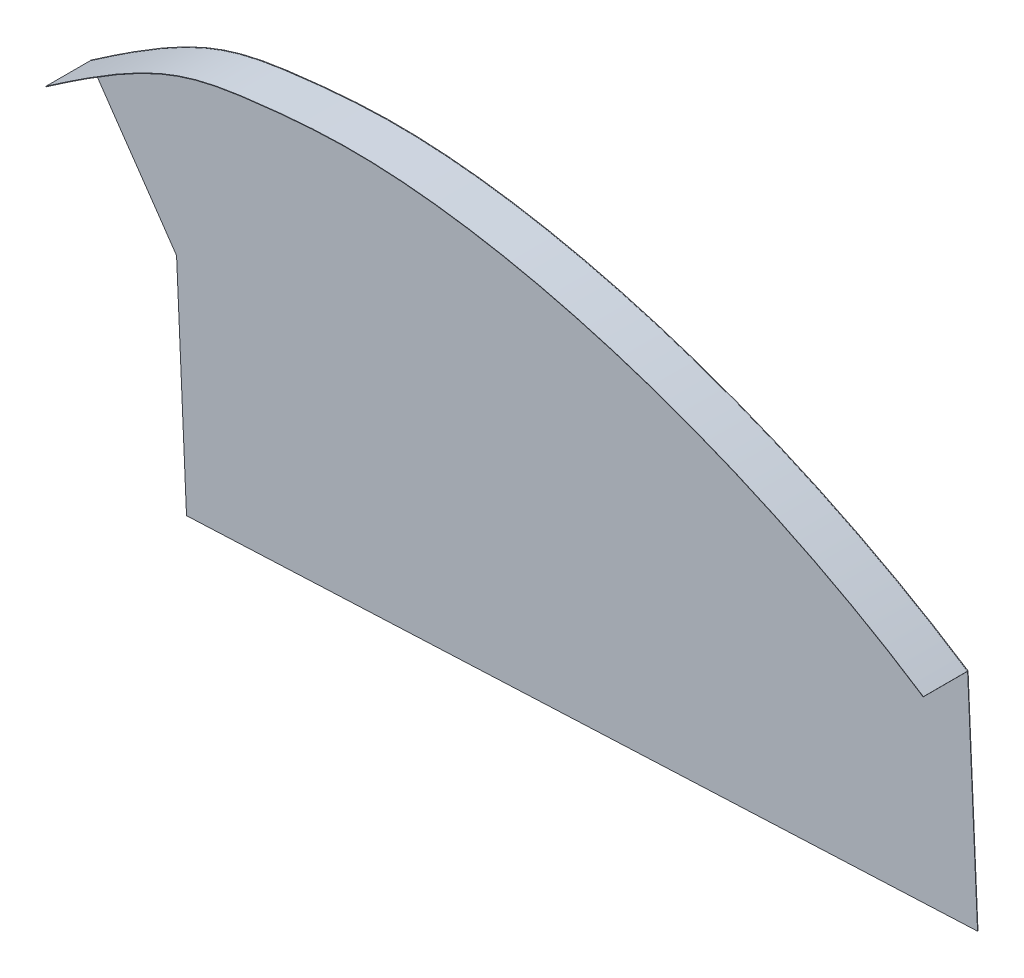
SolidWorks part; units mm, degrees
ref_plane "Front Plane" through (0, 0, 0) normal (0, 0, 1) x (1, 0, 0)
ref_plane "Top Plane" through (0, 0, 0) normal (0, 1, 0) x (1, 0, 0)
ref_plane "Right Plane" through (0, 0, 0) normal (1, 0, 0) x (0, 0, -1)
sketch "Sketch1" plane through (0, 0, 0) normal (0, 0, 1) x (1, 0, 0)
  line L0 (-169.0031, 11.7142) -> (-694.187, 895.1707) construction
  line L1 (-1544.65, 573.4414) -> (-1542.3973, 523.4922)
  line L2 (-1743.608, 593.8305) -> (-1723.9756, 565.3542)
  line L3 (-1544.65, 573.4414) -> (-1723.9756, 565.3542) construction
  line L4 (-1723.9756, 565.3542) -> (-1721.723, 515.405)
  line L5 (-1542.3973, 523.4922) -> (-1721.723, 515.405)
  spline S0 degree 3 poles (-1743.608, 593.8305) (-1719.5079, 610.5378) (-1709.3895, 613.3998) (-1646.2803, 619.2418) (-1585.7166, 600.4239) (-1544.65, 573.4414) knots 0 0 0 0 0.320555 0.420555 1 1 1 1
  point P6 (-1749.4095, 514.1564)
  point P7 (-864.9195, 554.0451)
  dimension "D1" = 200
extrude "Boss-Extrude1" add sketch "Sketch1" along normal blind 0.1
sketch "Sketch2" plane through (0, 0, 0.1) normal (0, 0, 1) x (1, 0, 0)
  line L0 (-1743.5795, 593.7894) -> (-1743.5225, 593.7072)
  line L1 (-1743.5225, 593.7072) -> (-1743.5258, 593.705)
  line L2 (-1544.6774, 573.3996) -> (-1544.7323, 573.3161)
  spline S0 degree 1 poles (-1544.7323, 573.3161) (-1743.5225, 593.7072) knots 0 0 1 1 construction
  spline S1 degree 3 poles (-1544.7323, 573.3161) (-1546.9519, 574.7745) (-1551.4313, 577.6136) (-1560.6294, 583.0453) (-1572.4709, 589.3269) (-1587.0699, 596.0193) (-1606.8127, 603.7551) (-1626.6209, 609.6253) (-1645.7855, 613.4616) (-1659.664, 615.2751) (-1672.8554, 616.0005) (-1683.1758, 615.6072) (-1690.7192, 614.94) (-1697.6194, 614.1843) (-1704.9414, 613.1758) (-1711.5371, 611.5206) (-1716.9507, 609.4963) (-1721.2263, 607.5471) (-1725.8618, 605.0871) (-1730.1444, 602.545) (-1733.8948, 600.1759) (-1736.8861, 598.2226) (-1739.5484, 596.4355) (-1741.7757, 594.9144) (-1742.9458, 594.107) (-1743.5225, 593.7072) knots 0 0 0 0 0.03125 0.0625 0.125 0.1875 0.25 0.375 0.4375 0.5 0.5625 0.625 0.65625 0.6875 0.75 0.8125 0.84375 0.875 0.90625 0.9375 0.953125 0.96875 0.984375 0.992188 1 1 1 1
  spline S2 degree 3 poles (-4441.9843, 53.111) (-858.6316, 47.5626) (-1418.7636, 592.69) (-1664.0556, 615.6153) (-1668.4586, 615.8535) (-1674.8505, 615.9246) (-1676.9471, 615.8989) (-1681.054, 615.7601) (-1685.0709, 615.538) (-1688.8415, 615.2069) (-1692.4557, 614.85) (-1694.1826, 614.66) (-1699.0922, 614.0849) (-1702.0267, 613.6789) (-1710.3915, 612.0761) (-1715.3828, 610.4946) (-1786.107, 575.5005) (-1964.3017, 381.9149) (-4240.6287, -1067.9648) knots -2.83274 -2.83274 -2.83274 -2.83274 0.5 0.5 0.5625 0.5625 0.59375 0.59375 0.625 0.65625 0.65625 0.6875 0.6875 0.75 0.75 0.875 0.875 2.236338 2.236338 2.236338 2.236338 only from (-1544.6774, 573.3996) to (-1743.5795, 593.7894)
  spline S3 degree 3 poles (-1544.6774, 573.3996) (-1580.1063, 596.6779) (-1623.4173, 611.8172) (-1664.0556, 615.6153) (-1668.4586, 615.8535) (-1674.8505, 615.9246) (-1676.9471, 615.8989) (-1681.054, 615.7601) (-1685.0709, 615.538) (-1688.8415, 615.2069) (-1692.4557, 614.85) (-1694.1826, 614.66) (-1699.0922, 614.0849) (-1702.0267, 613.6789) (-1710.3915, 612.0761) (-1715.3828, 610.4946) (-1727.2785, 604.6086) (-1734.1826, 600.3037) (-1743.5795, 593.7894) knots 0 0 0 0 0.5 0.5 0.5625 0.5625 0.59375 0.59375 0.625 0.65625 0.65625 0.6875 0.6875 0.75 0.75 0.875 0.875 1 1 1 1
  dimension "D1" = 0.05
  dimension "D2" = 0.1
extrude "Boss-Extrude2" add sketch "Sketch2" along normal blind 10 contours L2 S3 L0 S1
